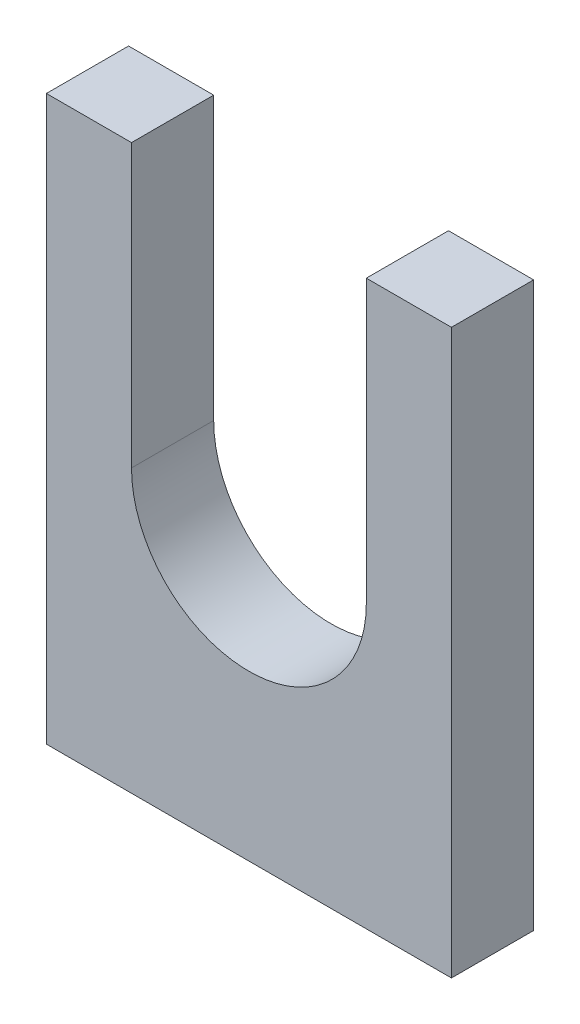
SolidWorks part; units mm, degrees
ref_plane "Front Plane" through (0, 0, 0) normal (0, 0, 1) x (1, 0, 0)
ref_plane "Top Plane" through (0, 0, 0) normal (0, 1, 0) x (1, 0, 0)
ref_plane "Right Plane" through (0, 0, 0) normal (1, 0, 0) x (0, 0, -1)
sketch "Sketch1" plane through (0, 0, 0) normal (0, 0, 1) x (1, 0, 0)
  line L0 (0, 12) -> (0, 0)
  line L1 (0, 0) -> (8.625, 0)
  line L2 (8.625, 0) -> (8.625, 12)
  line L3 (8.625, 12) -> (6.8125, 12)
  line L4 (0, 12) -> (1.8125, 12)
  line L5 (1.8125, 12) -> (1.8125, 6)
  line L6 (6.8125, 6) -> (6.8125, 12)
  arc A0 (6.8125, 6) -> (1.8125, 6) centre (4.3125, 6) cw
  dimension "D1" = 8.625
  dimension "D2" = 12
  dimension "D3" = 5
  dimension "D4" = 6
extrude "Boss-Extrude1" add sketch "Sketch1" along normal blind 1.75
scale "Scale1" scale about centroid uniform scaling yes scale factor 25.4
